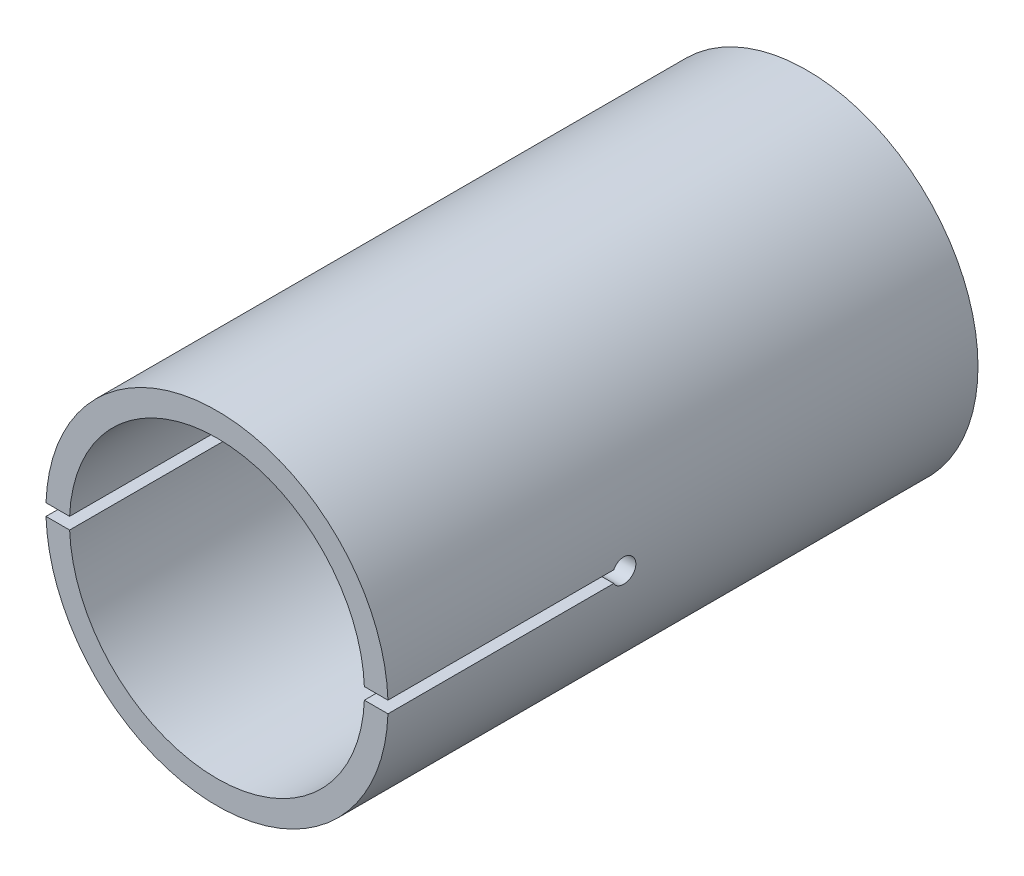
SolidWorks part; units mm, degrees
ref_plane "Ebene vorne" through (0, 0, 0) normal (0, 0, 1) x (1, 0, 0)
ref_plane "Ebene oben" through (0, 0, 0) normal (0, 1, 0) x (1, 0, 0)
ref_plane "Ebene rechts" through (0, 0, 0) normal (1, 0, 0) x (0, 0, -1)
sketch "Skizze1" plane through (0, 0, 0) normal (0, 0, 1) x (1, 0, 0)
  circle A2 centre (0, 0) radius 14.5
  dimension "D2" = 29
extrude "Aufsatz-Linear austragen1" add sketch "Skizze1" along normal blind 50
sketch "Skizze5" plane through (0, 0, 0) normal (0, 0, -1) x (-1, 0, 0)
  line L0 (-1.6, 7.8) -> (1.6, 7.8)
  line L1 (1.6, 7.8) -> (1.6, 5.8)
  line L2 (-1.6, 7.8) -> (-1.6, 5.8)
  line L3 (1.6, 5.8) -> (-1.6, 5.8)
  dimension "D1" = 3.2
  dimension "D2" = 2
  dimension "D3" = 7.8
  dimension "D4" = 1.6
extrude "Schnitt-Linear austragen1" cut sketch "Skizze5" against normal blind 25
hole_wizard "Ø24.5 (24.5) Durchmesser Bohrung1" positions "Skizze7" profile "Skizze8" hole size "Ø24.5" standard "ANSI Metrisch" end condition through all
sketch "Skizze7" plane through (0, 0, 0) normal (0, 0, -1) x (-1, 0, 0)
  point P0 (0, 0)
sketch "Skizze8" plane through (0, 0, 0) normal (1, 0, 0) x (0, 1, 0)
  line L0 (0, 0) -> (0, 50)
  line L1 (0, 50) -> (6.25, 50)
  line L2 (6.25, 50) -> (6.25, 0)
  line L5 (6.25, 0) -> (0, 0)
  line L11 (0, -6.35) -> (0, 107.95) construction
  dimension "Bohrerdurchmesser" = 12.5
  dimension "Bohrungstiefe" = 50
hole_wizard "Ø24.5 (24.5) Durchmesser Bohrung2" positions "Skizze10" profile "Skizze11" hole size "Ø24.5" standard "ANSI Metrisch"
sketch "Skizze10" plane through (0, 0, 50) normal (0, 0, 1) x (1, 0, 0)
  point P0 (0, 0)
sketch "Skizze11" plane through (0, 0, 50) normal (1, 0, 0) x (0, -1, 0)
  line L0 (0, 0) -> (0, 37.5108)
  line L1 (0, 37.5108) -> (12.5, 30)
  line L2 (12.5, 30) -> (12.5, 0)
  line L5 (12.5, 0) -> (0, 0)
  line L10 (0, 37.5108) -> (-12.5, 30) construction
  line L11 (0, -6.35) -> (0, 107.95) construction
  dimension "Bohrerdurchmesser" = 25
  dimension "Bohrungstiefe" = 30
  dimension "Spitzenwinkel" = 118
sketch "Skizze12" plane through (0, 0, 50) normal (0, 0, 1) x (1, 0, 0)
  line L0 (0, 0) -> (17.7399, 0) construction
  line L1 (-14.4914, 0.5) -> (-12.49, 0.5)
  line L3 (-14.4914, -0.5) -> (-12.49, -0.5)
  line L4 (12.49, 0.5) -> (14.4914, 0.5)
  line L6 (12.49, -0.5) -> (14.4914, -0.5)
  circle A0 centre (0, 0) radius 14.5 construction
  circle A1 centre (0, 0) radius 12.5 construction
  arc A2 (-14.4914, 0.5) -> (-14.4914, -0.5) centre (0, 0) ccw
  arc A3 (-12.49, 0.5) -> (-12.49, -0.5) centre (0, 0) ccw
  arc A4 (14.4914, 0.5) -> (14.4914, -0.5) centre (0, 0) cw
  arc A5 (12.49, 0.5) -> (12.49, -0.5) centre (0, 0) cw
  dimension "D5" = 14.5
  dimension "D6" = 12.5
  dimension "D7" = 12.5
  dimension "D8" = 14.5
  dimension "D1" = 0.5
  dimension "D2" = 0.5
  dimension "D3" = 0.5
  dimension "D4" = 0
extrude "Schnitt-Linear austragen2" cut sketch "Skizze12" against normal blind 20
ref_plane "Ebene1" through (-14.5, 0, 30) normal (-1, 0, 0) x (0, 0, 1)
sketch "Skizze24" plane through (-14.5, 0, 30) normal (-1, 0, 0) x (0, 0, 1)
  line L0 (-3.4417, 0) -> (2.6271, 0)
  line L1 (0, 1.8196) -> (0, -1.7364)
  line L2 (20, 0.5) -> (20, 14.5) construction
  dimension "D1" = 20
hole_wizard "Ø2.0 (2) Durchmesser Bohrung11" positions "Skizze29" profile "Skizze28" hole size "Ø2.0" standard "ANSI Metrisch"
sketch "Skizze29" plane through (-14.5, 0, 30) normal (-1, 0, 0) x (0, 0, 1)
  point P0 (0, 0)
sketch "Skizze28" plane through (-14.5, 0, 30) normal (0, 1, 0) x (0, 0, 1)
  line L0 (0, 0) -> (0, 30.6009)
  line L1 (0, 30.6009) -> (1, 30)
  line L2 (1, 30) -> (1, 0)
  line L5 (1, 0) -> (0, 0)
  line L10 (0, 30.6009) -> (-1, 30) construction
  line L11 (0, -6.35) -> (0, 107.95) construction
  dimension "Bohrerdurchmesser" = 2
  dimension "Bohrungstiefe" = 30
  dimension "Spitzenwinkel" = 118
